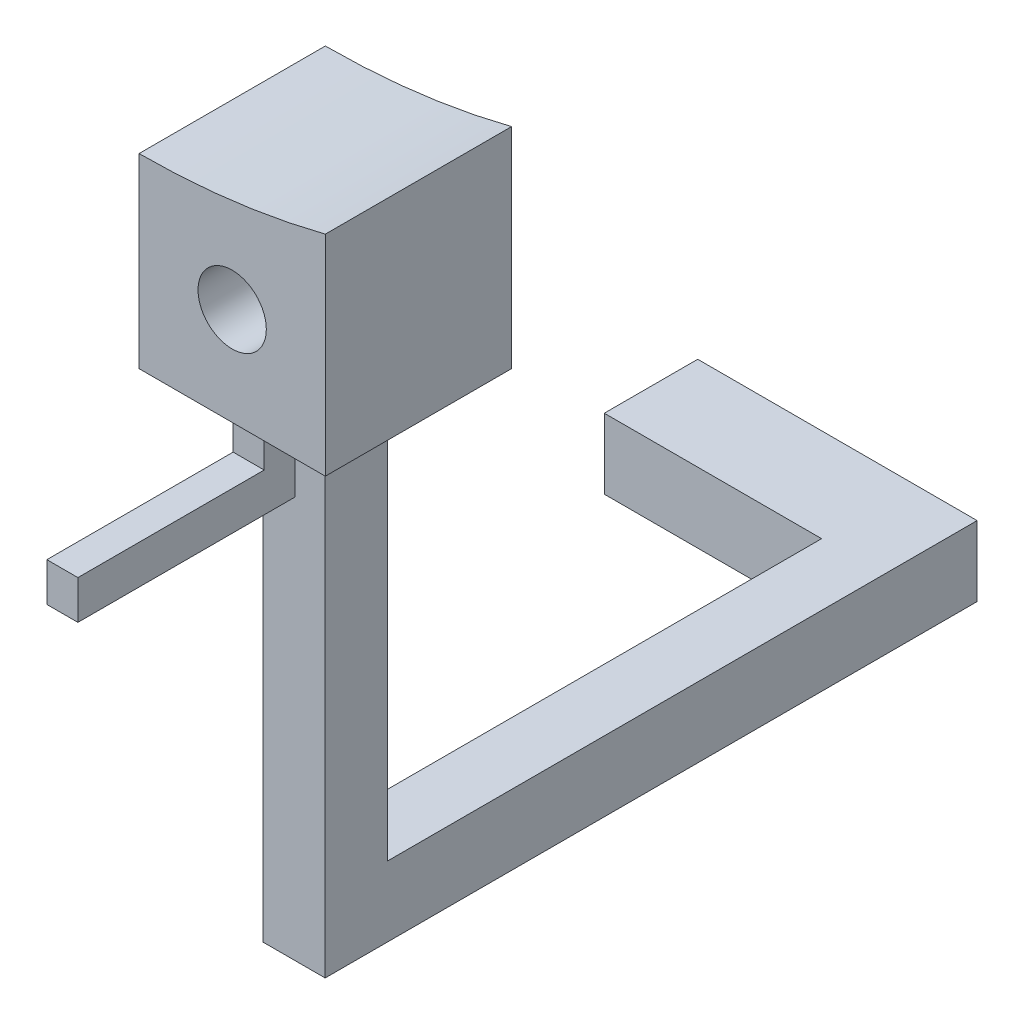
SolidWorks part; units mm, degrees
material "ABS PC"
ref_plane "Front Plane" through (0, 0, 0) normal (0, 0, 1) x (1, 0, 0)
ref_plane "Top Plane" through (0, 0, 0) normal (0, 1, 0) x (1, 0, 0)
ref_plane "Right Plane" through (0, 0, 0) normal (1, 0, 0) x (0, 0, -1)
sketch "Sketch1" plane through (0, 0, 0) normal (0, 0, 1) x (1, 0, 0)
  line L0 (0, -24.3) -> (0, -30.3)
  line L1 (0, -30.3) -> (6, -30.3)
  line L2 (6, -30.3) -> (6, -23.5476)
  arc A0 (0, -24.3) -> (6, -23.5476) centre (0, 0) ccw
  circle A1 centre (3, -27.1521) radius 1.1
  dimension "D1" = 6
  dimension "D2" = 2.2
  dimension "D3" = 6
extrude "Boss-Extrude1" add sketch "Sketch1" along normal blind 6
sketch "Sketch2" plane through (0, -30.3, 0) normal (0, -1, 0) x (1, 0, 0)
  line L0 (1.995, 4) -> (1.995, 6)
  line L1 (1.995, 2) -> (3.995, 2)
  line L2 (1.995, 2) -> (1.995, 4)
  line L3 (1.995, 4) -> (3.995, 4)
  line L4 (3.995, 2) -> (3.995, 4)
  line L5 (1.995, 2) -> (3.995, 4) construction
  line L6 (1.995, 4) -> (3.995, 2) construction
  line L7 (0, 6) -> (6, 6) construction
  point P0 (2.995, 3)
  dimension "D1" = 2
  dimension "D2" = 2
  dimension "D3" = 2
extrude "Boss-Extrude2" add sketch "Sketch2" along normal blind 16 contours L1 L4 L3 L2
sketch "Sketch4" plane through (0, 0, 2) normal (0, 0, -1) x (-1, 0, 0)
  line L0 (-3.995, -46.3) -> (-1.995, -46.3)
  line L19 (-1.995, -46.3) -> (-1.995, -34.3059)
  line L20 (-1.995, -46.3) -> (-1.995, -30.3) construction
  line L21 (-1.995, -34.3059) -> (-3.995, -34.3059)
  line L22 (-3.995, -46.3) -> (-3.995, -30.3) construction
  line L23 (-3.995, -34.3059) -> (-3.995, -46.3)
extrude "Boss-Extrude4" add sketch "Sketch4" along normal blind 19
sketch "Sketch5" plane through (0, -30.3, 0) normal (0, -1, 0) x (1, 0, 0)
  line L1 (2.5935, 4.5626) -> (3.5935, 4.5626)
  line L2 (2.5935, 4.5626) -> (2.5935, 5.5626)
  line L3 (2.5935, 5.5626) -> (3.5935, 5.5626)
  line L4 (3.5935, 4.5626) -> (3.5935, 5.5626)
  line L5 (2.5935, 4.5626) -> (3.5935, 5.5626) construction
  line L6 (2.5935, 5.5626) -> (3.5935, 4.5626) construction
  point P0 (3.0935, 5.0626)
  dimension "D1" = 1
  dimension "D2" = 1
extrude "Boss-Extrude5" add sketch "Sketch5" along normal blind 2.5
sketch "Sketch6" plane through (0, 0, 5.5626) normal (0, 0, 1) x (1, 0, 0)
  line L0 (2.5935, -32.8) -> (3.5935, -32.8)
  line L1 (3.5935, -32.8) -> (3.5935, -31.55)
  line L2 (3.5935, -32.8) -> (3.5935, -30.3) construction
  line L3 (3.5935, -31.55) -> (2.5935, -31.55)
  line L4 (2.5935, -32.8) -> (2.5935, -30.3) construction
  line L5 (2.5935, -31.55) -> (2.5935, -32.8)
extrude "Boss-Extrude6" add sketch "Sketch6" along normal blind 6
sketch "Sketch7" plane through (1.995, 0, 0) normal (-1, 0, 0) x (0, 0, 1)
  line L0 (-17, -46.3) -> (-17, -34.3059)
  line L1 (-17, -34.3059) -> (-13.9906, -34.3059)
  line L2 (-17, -34.3059) -> (2, -34.3059) construction
  line L3 (-13.9906, -34.3059) -> (-13.9906, -46.3)
  line L4 (-17, -46.3) -> (4, -46.3) construction
  line L5 (-13.9906, -46.3) -> (-17, -46.3)
extrude "Boss-Extrude7" add sketch "Sketch7" along normal blind 7
sketch "Sketch8" plane through (0, 0, 0) normal (0, 0, -1) x (-1, 0, 0)
  circle A0 centre (-3, -27.1521) radius 1.1
extrude "Boss-Extrude8" add sketch "Sketch8" against normal blind 1
sketch "Sketch9" plane through (0, 0, 6) normal (0, 0, 1) x (1, 0, 0)
  circle A0 centre (3, -27.1521) radius 1.1
extrude "Cut-Extrude1" cut sketch "Sketch9" against normal blind 10
sketch "Sketch10" plane through (-5.005, 0, 0) normal (-1, 0, 0) x (0, 0, 1)
  line L0 (-17, -34.3059) -> (2, -34.3059)
  line L1 (2, -34.3059) -> (2, -44.0404)
  line L2 (2, -44.0404) -> (-17, -44.0404)
  line L3 (-17, -34.3059) -> (-17, -46.3) construction
  line L4 (-17, -44.0404) -> (-17, -34.3059)
extrude "Cut-Extrude2" cut sketch "Sketch10" against normal blind 10
